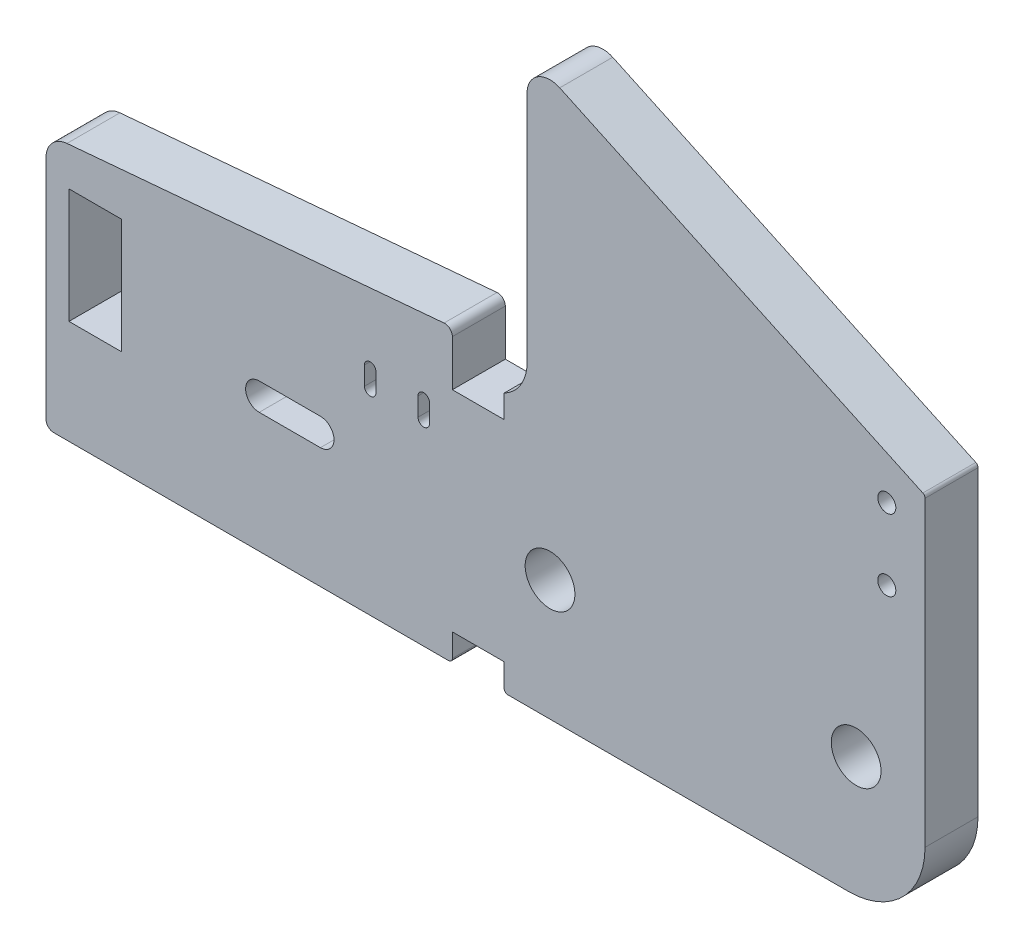
SolidWorks part; units mm, degrees
ref_plane "Front Plane" through (0, 0, 0) normal (0, 0, 1) x (1, 0, 0)
ref_plane "Top Plane" through (0, 0, 0) normal (0, 1, 0) x (1, 0, 0)
ref_plane "Right Plane" through (0, 0, 0) normal (1, 0, 0) x (0, 0, -1)
sketch "Sketch1" plane through (0, 0, 0) normal (0, 0, 1) x (1, 0, 0)
  line L0 (50.108, 27.95) -> (50.108, 25.55)
  line L1 (48.608, 25.55) -> (48.608, 27.95)
  line L2 (43.108, 27.95) -> (43.108, 25.55)
  line L3 (41.608, 25.55) -> (41.608, 27.95)
  line L4 (35.858, 15.725) -> (27.858, 15.725)
  line L5 (27.858, 19.275) -> (35.858, 19.275)
  line L6 (114.858, 10) -> (114.858, 49.5)
  line L7 (114.5693, 49.9532) -> (67.1259, 72.0764)
  line L8 (62.858, 69.3575) -> (62.858, 38.8303)
  line L9 (59.858, 33.9) -> (59.858, 30.9)
  line L10 (59.858, 30.9) -> (53.098, 30.9)
  line L11 (53.098, 30.9) -> (53.098, 36.9087)
  line L12 (52.0108, 37.9049) -> (2.7385, 33.5941)
  line L13 (0, 30.6055) -> (0, 1)
  line L14 (1, 0) -> (52.598, 0)
  line L15 (53.098, 0.5) -> (53.098, 3.5)
  line L16 (53.098, 3.5) -> (59.858, 3.5)
  line L17 (59.858, 3.5) -> (59.858, 0.5)
  line L18 (60.358, 0) -> (104.858, 0)
  line L19 (9.858, 28.584) -> (3, 28.584)
  line L20 (3, 28.584) -> (3, 13.584)
  line L21 (3, 13.584) -> (9.858, 13.584)
  line L22 (9.858, 13.584) -> (9.858, 28.584)
  circle A0 centre (65.858, 15.75) radius 3.25
  circle A1 centre (105.858, 15.75) radius 3.25
  circle A2 centre (109.858, 37.1528) radius 1.1811
  circle A3 centre (109.858, 46.5) radius 1.1811
  arc A4 (48.608, 25.55) -> (50.108, 25.55) centre (49.358, 25.55) ccw
  arc A5 (50.108, 27.95) -> (48.608, 27.95) centre (49.358, 27.95) ccw
  arc A6 (41.608, 25.55) -> (43.108, 25.55) centre (42.358, 25.55) ccw
  arc A7 (43.108, 27.95) -> (41.608, 27.95) centre (42.358, 27.95) ccw
  arc A8 (27.858, 19.275) -> (27.858, 15.725) centre (27.858, 17.5) ccw
  arc A9 (35.858, 15.725) -> (35.858, 19.275) centre (35.858, 17.5) ccw
  arc A10 (104.858, 0) -> (114.858, 10) centre (104.858, 10) ccw
  arc A11 (114.858, 49.5) -> (114.5693, 49.9532) centre (114.358, 49.5) ccw
  arc A12 (67.1259, 72.0764) -> (62.858, 69.3575) centre (65.858, 69.3575) ccw
  arc A13 (59.858, 33.9) -> (62.858, 38.8303) centre (57.3068, 38.8303) ccw
  arc A14 (53.098, 36.9087) -> (52.0108, 37.9049) centre (52.098, 36.9087) ccw
  arc A15 (2.7385, 33.5941) -> (0, 30.6055) centre (3, 30.6055) ccw
  arc A16 (0, 1) -> (1, 0) centre (1, 1) ccw
  arc A17 (52.598, 0) -> (53.098, 0.5) centre (52.598, 0.5) ccw
  arc A18 (59.858, 0.5) -> (60.358, 0) centre (60.358, 0.5) ccw
extrude "Boss-Extrude1" add sketch "Sketch1" along normal blind 6.92
